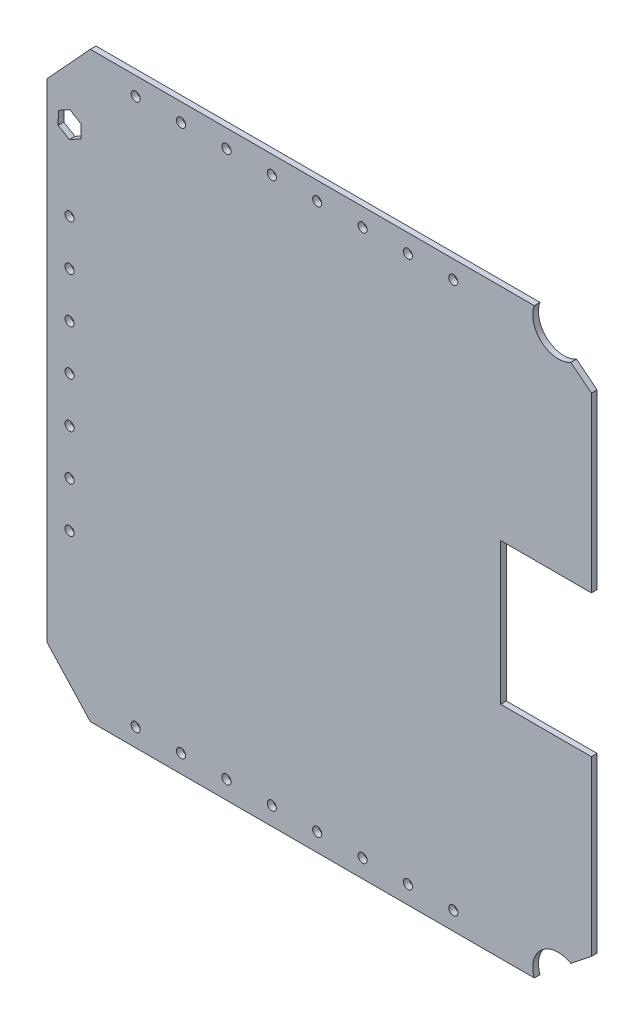
SolidWorks part; units mm, degrees
ref_plane "Front Plane" through (0, 0, 0) normal (0, 0, 1) x (1, 0, 0)
ref_plane "Top Plane" through (0, 0, 0) normal (0, 1, 0) x (1, 0, 0)
ref_plane "Right Plane" through (0, 0, 0) normal (1, 0, 0) x (0, 0, -1)
sketch "Sketch1" plane through (0, 0, 0) normal (0, 0, 1) x (1, 0, 0)
  line L0 (-152.4, 136.525) -> (-128.098, 162.977)
  line L1 (152.4, -39.6875) -> (152.4, -136.525)
  line L2 (-152.4, 136.525) -> (-152.4, -136.525)
  line L3 (140.8749, -145.6693) -> (152.4, -136.525)
  line L4 (152.4, 136.525) -> (152.4, 39.6875)
  line L5 (-152.4, 136.525) -> (152.4, -136.525) construction
  line L6 (-152.4, -136.525) -> (152.4, 136.525) construction
  line L7 (152.4, -39.6875) -> (101.6, -39.6875)
  line L8 (-128.098, 162.977) -> (120.4232, 162.977)
  line L9 (152.4, 39.6875) -> (101.6, 39.6875)
  line L10 (101.6, -39.6875) -> (101.6, 39.6875)
  line L11 (-152.4, 0) -> (152.4, 0) construction
  line L13 (140.8749, 145.6693) -> (152.4, 136.525)
  line L14 (-128.098, -162.977) -> (120.4232, -162.977)
  line L15 (-152.4, -136.525) -> (-128.098, -162.977)
  arc A0 (120.4232, 162.977) -> (140.8749, 145.6693) centre (133.858, 158.115) ccw
  arc A2 (120.4232, -162.977) -> (140.8749, -145.6693) centre (133.858, -158.115) cw
  point P0 (0, 0)
  dimension "D10" = 21.59
  dimension "D11" = 18.542
  dimension "D12" = 28.575
  dimension "D1" = 273.05
  dimension "D2" = 304.8
  dimension "D3" = 50.8
  dimension "D4" = 79.375
  dimension "D5" = 96.8375
  dimension "D6" = 14.7121
  dimension "D7" = 35.9207
  dimension "D9" = 96.8375
  dimension "D15" = 248.5212
extrude "Boss-Extrude1" add sketch "Sketch1" along normal blind 3.175
sketch "Sketch2" plane through (0, 0, 3.175) normal (0, 0, 1) x (1, 0, 0)
  line L0 (-102.698, 152.8297) -> (-77.298, 152.8297) construction
  line L1 (-152.4, 0) -> (101.6, 0) construction
  line L2 (-152.4, 136.525) -> (-152.4, -136.525) construction
  line L3 (101.6, -39.6875) -> (101.6, 39.6875) construction
  circle A0 centre (-102.698, 152.8297) radius 2.5527
  circle A1 centre (-77.298, 152.8297) radius 2.5527
  circle A2 centre (-51.898, 152.8297) radius 2.5527
  circle A3 centre (-26.498, 152.8297) radius 2.5527
  circle A4 centre (-1.098, 152.8297) radius 2.5527
  circle A5 centre (24.302, 152.8297) radius 2.5527
  circle A6 centre (49.702, 152.8297) radius 2.5527
  circle A7 centre (75.102, 152.8297) radius 2.5527
  circle A9 centre (-51.898, -152.8297) radius 2.5527
  circle A10 centre (-77.298, -152.8297) radius 2.5527
  circle A11 centre (-102.698, -152.8297) radius 2.5527
  circle A12 centre (-26.498, -152.8297) radius 2.5527
  circle A13 centre (-1.098, -152.8297) radius 2.5527
  circle A14 centre (24.302, -152.8297) radius 2.5527
  circle A15 centre (49.702, -152.8297) radius 2.5527
  circle A16 centre (75.102, -152.8297) radius 2.5527
  circle A18 centre (100.502, 152.8297) radius 2.5527 [skipped]
  dimension "D3" = 5.1054
  dimension "D1" = 12.7
  dimension "D2" = 25.4
  dimension "D5" = 25.4
  dimension "D4" = 9
extrude "Cut-Extrude1" cut sketch "Sketch2" against normal through all
sketch "Sketch3" plane through (0, 0, 3.175) normal (0, 0, 1) x (1, 0, 0)
  line L0 (-152.4, 136.525) -> (-152.4, -136.525) construction
  line L1 (-133.287, 124.2048) -> (-139.572, 127.9812)
  line L2 (-139.572, 127.9812) -> (-145.985, 124.4264)
  line L3 (-145.985, 124.4264) -> (-146.113, 117.0952)
  line L4 (-146.113, 117.0952) -> (-139.828, 113.3188)
  line L5 (-139.828, 113.3188) -> (-133.415, 116.8736)
  line L6 (-133.415, 116.8736) -> (-133.287, 124.2048)
  circle A0 centre (-139.7, 120.65) radius 6.35 construction
  dimension "D3" = 12.7
  dimension "D1" = 15.875
  dimension "D2" = 12.7
  dimension "D4" = 1
extrude "Cut-Extrude2" cut sketch "Sketch3" against normal through all
sketch "Sketch4" plane through (0, 0, 0) normal (0, 0, -1) x (-1, 0, 0)
  line L0 (139.7, 76.2) -> (139.7, 50.8) construction
  circle A0 centre (139.7, 76.2) radius 2.5527
  circle A1 centre (139.7, 50.8) radius 2.5527
  circle A2 centre (139.7, 25.4) radius 2.5527
  circle A3 centre (139.7, 0) radius 2.5527
  circle A4 centre (139.7, -25.4) radius 2.5527
  circle A5 centre (139.7, -50.8) radius 2.5527
  circle A6 centre (139.7, -76.2) radius 2.5527
  dimension "D1" = 5.1054
  dimension "D2" = 60.325
  dimension "D3" = 12.7
  dimension "D5" = 25.4
  dimension "D4" = 7
extrude "Cut-Extrude3" cut sketch "Sketch4" against normal through all
sketch "Sketch5" plane through (0, 0, 0) normal (0, 0, -1) x (-1, 0, 0)
  line L1 (100.7048, 120.0863) -> (18.1548, 120.0863)
  line L2 (100.7048, 120.0863) -> (100.7048, 24.8363)
  line L3 (100.7048, 24.8363) -> (18.1548, 24.8363)
  line L4 (18.1548, 120.0863) -> (18.1548, 24.8363)
  line L5 (100.7048, -26.3822) -> (18.2699, -26.3822)
  line L6 (100.7048, -26.3822) -> (100.7048, -118.0552)
  line L7 (100.7048, -118.0552) -> (18.2699, -118.0552)
  line L8 (18.2699, -26.3822) -> (18.2699, -118.0552)
  line L9 (0, 110.845) -> (-65.2317, 110.845)
  line L10 (0, 110.845) -> (0, -7.3901)
  line L11 (0, -7.3901) -> (-65.2317, -7.3901)
  line L12 (-65.2317, 110.845) -> (-65.2317, -7.3901)
  line L13 (-7.0316, -26.3822) -> (-65.2317, -26.3822)
  line L14 (-7.0316, -26.3822) -> (-7.0316, -126.0669)
  line L15 (-7.0316, -126.0669) -> (-65.2317, -126.0669)
  line L16 (-65.2317, -26.3822) -> (-65.2317, -126.0669)
  dimension "D1" = 95.25
  dimension "D2" = 82.55
